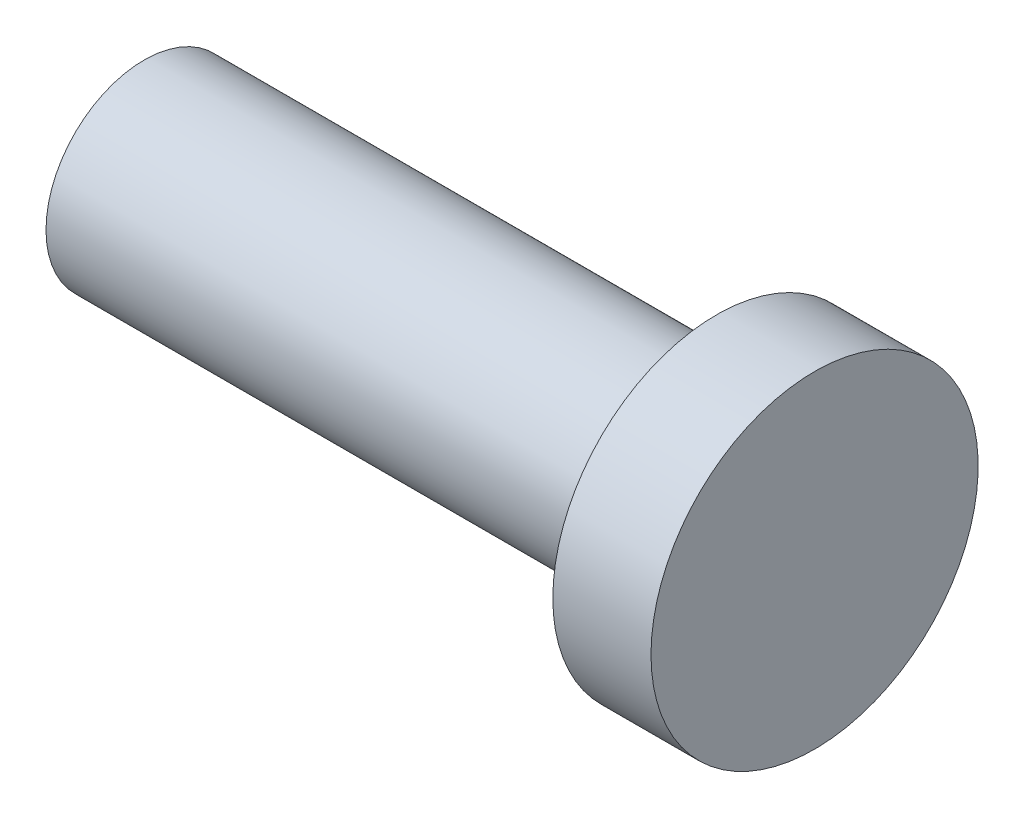
SolidWorks part; units mm, degrees
ref_plane "Front Plane" through (0, 0, 0) normal (0, 0, 1) x (1, 0, 0)
ref_plane "Top Plane" through (0, 0, 0) normal (0, 1, 0) x (1, 0, 0)
ref_plane "Right Plane" through (0, 0, 0) normal (1, 0, 0) x (0, 0, -1)
sketch "Sketch1" plane through (0, 0, 0) normal (0, 1, 0) x (1, 0, 0)
  line L0 (-42.2102, 0) -> (49.9571, 0) construction
  line L1 (0, 0) -> (0, 2.5) construction
  line L2 (-1.5, 2.5) -> (-1.5, 1.5) construction
  line L3 (-1.5, 1.5) -> (-10.2455, 1.5) construction
  line L4 (-10.2455, 1.5) -> (-10.2455, 0) construction
  line L5 (-10.2455, 0) -> (0, 0) construction
  line L6 (0, 0) -> (0, 2.5)
  line L7 (0, 2.5) -> (-1.5, 2.5)
  line L8 (-1.5, 2.5) -> (-1.5, 1.5)
  line L9 (-1.5, 1.5) -> (-10.2455, 1.5)
  line L10 (-10.2455, 1.5) -> (-10.2455, 0)
  line L11 (-10.2455, 0) -> (0, 0)
  dimension "D1" = 1.5
  dimension "D2" = 2.5
  dimension "D3" = 1.5
revolve "Revolve1" add sketch "Sketch1" angle 360 about L0
